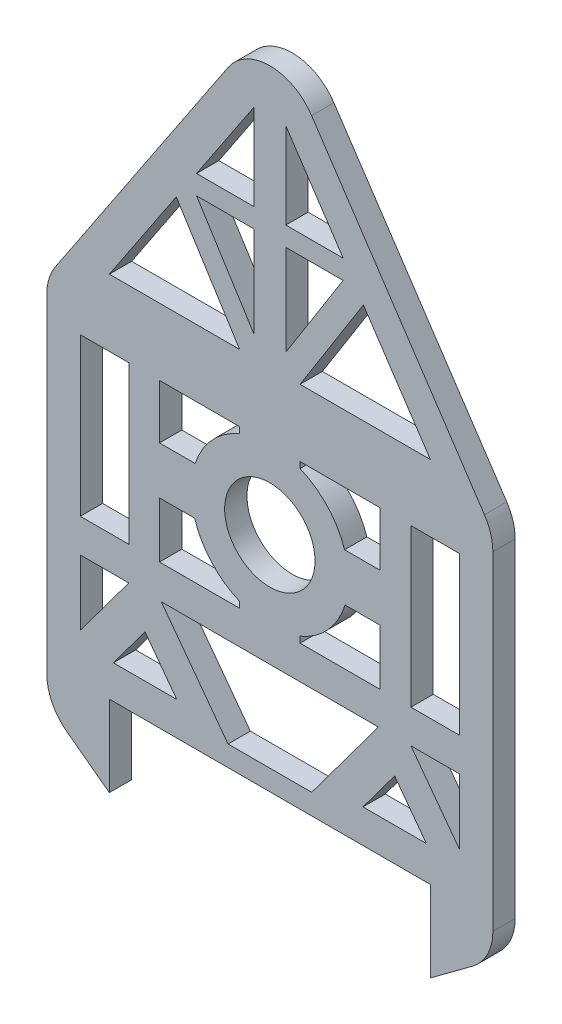
SolidWorks part; units mm, degrees
ref_plane "Front Plane" through (0, 0, 0) normal (0, 0, 1) x (1, 0, 0)
ref_plane "Top Plane" through (0, 0, 0) normal (0, 1, 0) x (1, 0, 0)
ref_plane "Right Plane" through (0, 0, 0) normal (1, 0, 0) x (0, 0, -1)
sketch "Sketch1" plane through (0, 0, 0) normal (0, 0, 1) x (1, 0, 0)
  line L0 (-324.5, 0) -> (-36.6111, 0)
  line L1 (19.4444, 0) -> (19.4444, 300)
  line L2 (19.4444, 300) -> (-180.5556, 600)
  line L3 (-180.5556, 600) -> (-380.5556, 300)
  line L4 (-380.5556, 300) -> (-380.5556, 0)
  line L5 (-380.5556, 0) -> (-380.5556, -30.9894)
  line L6 (19.4444, 300) -> (25, 294.4444)
  line L7 (-350.5556, 98.9559) -> (-307.0461, 98.9559)
  line L8 (-350.5556, 40.385) -> (-307.0461, 98.9559)
  line L9 (-218.053, 18.3812) -> (-277.9079, 98.9559)
  line L10 (-143.0581, 18.3812) -> (-83.2032, 98.9559)
  line L11 (-40.2128, 30) -> (-97.0554, 30)
  line L12 (-350.5556, 128.9559) -> (-307.0461, 128.9559)
  line L13 (-194.896, 524.4061) -> (-246.3088, 447.2869)
  line L14 (-36.6111, 330) -> (-96.6333, 420.0334)
  line L15 (-324.5, 330) -> (-207.6471, 330)
  line L16 (-10.5556, 40.385) -> (-54.065, 98.9559)
  line L17 (-180.5556, 545.9167) -> (-355.594, 283.359) construction
  line L18 (-5.5171, 283.359) -> (-180.5556, 545.9167) construction
  line L19 (-350.5556, 270) -> (-307.0461, 270)
  line L20 (-350.5556, 270) -> (-350.5556, 221.4578)
  line L21 (-10.5556, 128.9559) -> (-10.5556, 178.791)
  line L22 (-350.5556, 300) -> (-350.5556, 0) construction
  line L23 (-380.5556, -30.9894) -> (-324.5, -72.6302)
  line L24 (-380.5556, 128.9559) -> (19.4444, 128.9559) construction
  line L25 (-292.477, 115.7535) -> (-292.477, 91.7007) construction
  line L26 (-97.0554, 30) -> (-68.6341, 68.2598)
  line L27 (-218.053, 18.3812) -> (-143.0581, 18.3812)
  line L28 (-40.2128, 30) -> (-68.6341, 68.2598)
  line L29 (-320.8984, 30) -> (-264.0557, 30)
  line L30 (-153.464, 330) -> (-36.6111, 330)
  line L31 (-320.8984, 30) -> (-292.477, 68.2598)
  line L32 (-54.065, 98.9559) -> (-10.5556, 98.9559)
  line L33 (-277.9079, 98.9559) -> (-83.2032, 98.9559)
  line L34 (-264.0557, 30) -> (-292.477, 68.2598)
  line L35 (-380.5556, 98.9559) -> (19.4444, 98.9559) construction
  line L36 (-324.5, -72.6302) -> (-324.5, 0)
  line L37 (-36.6111, -72.6302) -> (-36.6111, 0)
  line L38 (-246.3088, 447.2869) -> (-194.896, 447.2869)
  line L41 (-180.5556, 424.8555) -> (-180.5556, 353.486) construction
  line L44 (-307.0461, 270) -> (-307.0461, 221.4578)
  line L45 (-279.5115, 270) -> (-279.5115, 221.4578)
  line L46 (-548.4441, 199.478) -> (-478.3267, 199.478) construction
  line L47 (-307.0461, 128.9559) -> (-307.0461, 178.791)
  line L48 (-279.5115, 128.9559) -> (-279.5115, 178.791)
  line L49 (19.4444, -30.9894) -> (-36.6111, -72.6302)
  line L50 (19.4444, 0) -> (19.4444, -30.9894)
  line L51 (-380.5556, 0) -> (-380.5556, -30.9894)
  line L52 (19.4444, 0) -> (19.4444, -30.9894)
  line L53 (-350.5556, 98.9559) -> (-350.5556, 40.385)
  line L54 (-10.5556, 98.9559) -> (-10.5556, 40.385)
  line L55 (-207.6471, 134.3673) -> (-207.6471, 128.9559)
  line L56 (-153.464, 134.3673) -> (-153.464, 128.9559)
  line L57 (-207.6471, 264.5887) -> (-207.6471, 270)
  line L58 (-153.464, 264.5887) -> (-153.464, 270)
  line L59 (-81.5996, 128.9559) -> (-81.5996, 178.791)
  line L60 (-54.065, 128.9559) -> (-54.065, 178.791)
  line L61 (-81.5996, 270) -> (-81.5996, 221.4578)
  line L62 (-54.065, 270) -> (-54.065, 221.4578)
  line L63 (-350.5556, 178.791) -> (-350.5556, 128.9559)
  line L64 (-114.8023, 429.9922) -> (-166.2152, 429.9922)
  line L65 (-114.8023, 447.2869) -> (-166.2152, 524.4061)
  line L66 (-194.896, 524.4061) -> (-194.896, 447.2869)
  line L67 (-166.2152, 524.4061) -> (-166.2152, 447.2869)
  line L68 (-246.3088, 429.9922) -> (-194.896, 348.542)
  line L69 (-264.4778, 420.0334) -> (-207.6471, 330)
  line L70 (-114.8023, 429.9922) -> (-166.2152, 348.542)
  line L71 (-96.6333, 420.0334) -> (-153.464, 330)
  line L72 (-166.2152, 447.2869) -> (-114.8023, 447.2869)
  line L73 (-194.896, 429.9922) -> (-246.3088, 429.9922)
  line L74 (-194.896, 429.9922) -> (-194.896, 348.542)
  line L75 (-166.2152, 429.9922) -> (-166.2152, 348.542)
  line L76 (-264.4778, 420.0334) -> (-324.5, 330)
  line L77 (-10.5556, 221.4578) -> (-10.5556, 270)
  line L78 (-81.5996, 178.791) -> (-113.1359, 178.791)
  line L79 (-81.5996, 221.4578) -> (-113.5463, 221.4578)
  line L80 (-279.5115, 178.791) -> (-247.9752, 178.791)
  line L81 (-279.5115, 221.4578) -> (-247.5648, 221.4578)
  line L82 (-279.5115, 270) -> (-207.6471, 270)
  line L83 (-279.5115, 128.9559) -> (-207.6471, 128.9559)
  line L84 (-54.065, 128.9559) -> (-10.5556, 128.9559)
  line L85 (-54.065, 270) -> (-10.5556, 270)
  line L86 (-153.464, 270) -> (-81.5996, 270)
  line L87 (-153.464, 128.9559) -> (-81.5996, 128.9559)
  line L88 (-10.5556, 221.4578) -> (-10.5556, 178.791)
  line L89 (-54.065, 221.4578) -> (-54.065, 178.791)
  line L90 (-307.0461, 221.4578) -> (-307.0461, 178.791)
  line L91 (-350.5556, 221.4578) -> (-350.5556, 178.791)
  arc A0 (-247.9752, 178.791) -> (-207.6471, 134.3673) centre (-180.5556, 199.478) ccw
  circle A1 centre (-180.5556, 199.478) radius 40.522
  arc A2 (-113.5463, 221.4578) -> (-153.464, 264.5887) centre (-180.5556, 199.478) ccw
  circle A3 centre (-180.5556, 199.478) radius 70.522 construction
  arc A4 (-207.6471, 264.5887) -> (-247.5648, 221.4578) centre (-180.5556, 199.478) ccw
  arc A5 (-153.464, 134.3673) -> (-113.1359, 178.791) centre (-180.5556, 199.478) ccw
  point P3 (-180.5556, 0)
  point P11 (-279.5115, 98.9559)
  point P13 (-81.5996, 98.9559)
  point P16 (-380.5556, 330)
  point P17 (19.4444, 330)
  point P23 (-10.5556, 0)
  point P24 (-10.5556, 300)
  point P25 (-380.5556, 270)
  point P26 (19.4444, 270)
  point P33 (-81.3793, 56.7498)
  point P34 (-1.5461, -21.4335)
  point P35 (-180.5556, -42.4264)
  point P36 (-279.7318, 56.7498)
  point P37 (-359.565, -21.4335)
  point P38 (-380.5556, 30)
  point P39 (19.4444, 30)
  point P69 (-307.0461, 153.8735)
  point P74 (-356.4732, -17.8896)
  point P83 (-54.065, 153.8735)
  point P93 (-113.115, 220.0966)
  point P112 (-282.9637, 81.0663)
  point P113 (-228.4809, -17.8896)
  point P114 (-301.9903, 81.0663)
  point P115 (-380.5556, 30)
  dimension "D3" = 400
  dimension "D8" = 53.393
  dimension "D4" = 30
  dimension "D5" = 30
  dimension "D7" = 30
  dimension "D9" = 30
extrude "Boss-Extrude1" add sketch "Sketch1" along normal blind 20 contours L50 L1 L2 L3 L4 L5 L23 L36 L0 L37 L49 A1 L91 L20 L19 L44 L90 L47 L12 L63 L89 L62 L85 L77 L88 L21 L84 L60 L76 L69 L15 L75 L64 L70 L72 L67 L65 L71 L14 L30 L53 L7 L8
fillet "Fillet1" radius 45 5 edges at (-380.5556, 300, 10) (-380.5556, -30.9894, 10) (19.4444, -30.9894, 10) (19.4444, 300, 10) (-180.5556, 600, 10)
